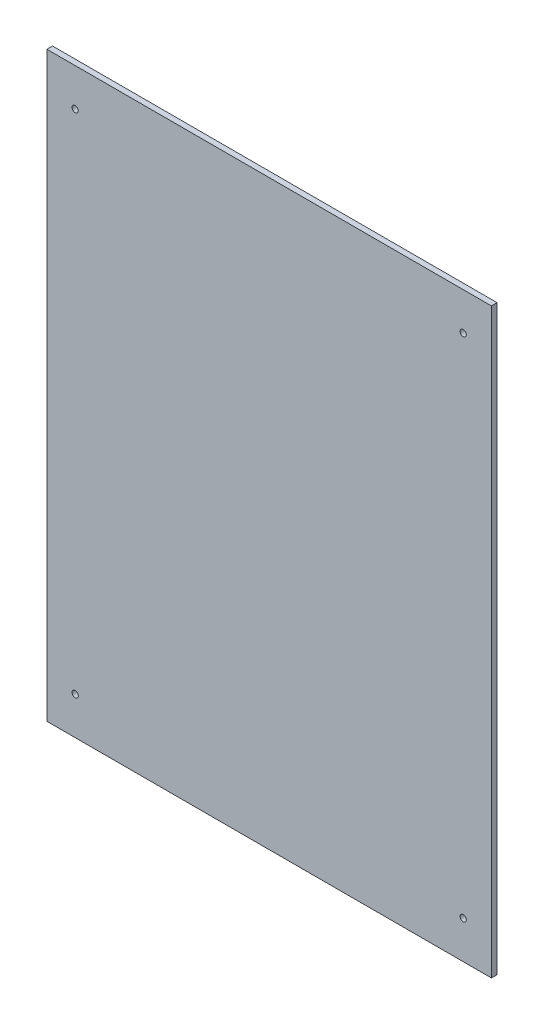
SolidWorks part; units mm, degrees
ref_plane "Plan de face" through (0, 0, 0) normal (0, 0, 1) x (1, 0, 0)
ref_plane "Plan de dessus" through (0, 0, 0) normal (0, 1, 0) x (1, 0, 0)
ref_plane "Plan de droite" through (0, 0, 0) normal (1, 0, 0) x (0, 0, -1)
sketch "Esquisse1" plane through (0, 0, 0) normal (0, 0, 1) x (1, 0, 0)
  line L1 (0, 0) -> (236, 0)
  line L2 (0, 0) -> (0, 309)
  line L3 (0, 309) -> (236, 309)
  line L4 (236, 0) -> (236, 309)
  dimension "D1" = 309
  dimension "D2" = 236
extrude "Boss.-Extru.1" add sketch "Esquisse1" along normal blind 3
sketch "Esquisse3" plane through (0, 0, 3) normal (0, 0, 1) x (1, 0, 0)
  line L1 (236, 309) -> (0, 309) construction
  line L2 (0, 0) -> (236, 0) construction
  line L4 (0, 309) -> (0, 0) construction
  line L6 (118, 154.5) -> (0, 154.5) construction
  line L7 (118, 309) -> (118, 0) construction
  circle A0 centre (15, 289) radius 1.65
  circle A1 centre (15, 20) radius 1.65
  circle A2 centre (221, 20) radius 1.65
  circle A3 centre (221, 289) radius 1.65
  dimension "D3" = 3.3
  dimension "D1" = 15
  dimension "D4" = 20
extrude "Enlèv. mat.-Extru.1" cut sketch "Esquisse3" against normal through all
